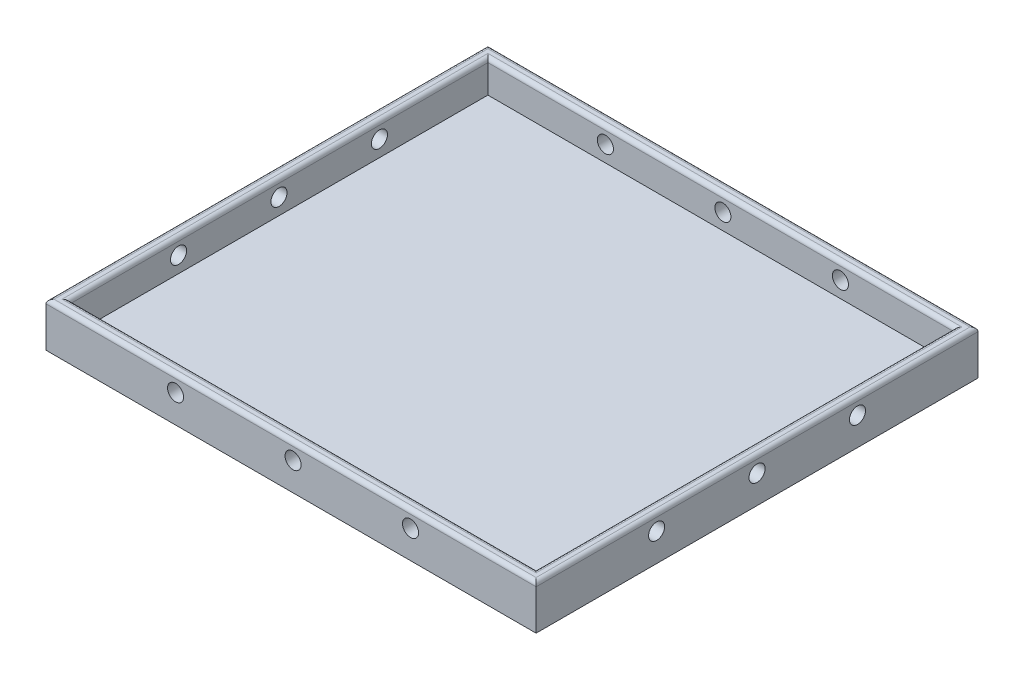
SolidWorks part; units mm, degrees
ref_plane "Front Plane" through (0, 0, 0) normal (0, 0, 1) x (1, 0, 0)
ref_plane "Top Plane" through (0, 0, 0) normal (0, 1, 0) x (1, 0, 0)
ref_plane "Right Plane" through (0, 0, 0) normal (1, 0, 0) x (0, 0, -1)
sketch "Sketch1" plane through (0, 0, 0) normal (0, 1, 0) x (1, 0, 0)
  line L1 (-201.6099, 77.8947) -> (-79.6099, 77.8947)
  line L2 (-201.6099, 77.8947) -> (-201.6099, -32.1053)
  line L3 (-201.6099, -32.1053) -> (-79.6099, -32.1053)
  line L4 (-79.6099, 77.8947) -> (-79.6099, -32.1053)
  dimension "D1" = 122
  dimension "D2" = 110
extrude "Boss-Extrude1" add sketch "Sketch1" along normal blind 11
sketch "Sketch4" plane through (0, 11, 0) normal (0, 1, 0) x (1, 0, 0)
  line L0 (-201.6099, 77.8947) -> (-201.6099, -32.1053) construction
  line L1 (-198.6099, 74.8947) -> (-82.6099, 74.8947)
  line L2 (-198.6099, 74.8947) -> (-198.6099, -29.1053)
  line L3 (-198.6099, -29.1053) -> (-82.6099, -29.1053)
  line L4 (-82.6099, 74.8947) -> (-82.6099, -29.1053)
  line L5 (-79.6099, 77.8947) -> (-201.6099, 77.8947) construction
  line L6 (-79.6099, -32.1053) -> (-79.6099, 77.8947) construction
  line L7 (-201.6099, -32.1053) -> (-79.6099, -32.1053) construction
  dimension "D1" = 3
  dimension "D2" = 3
  dimension "D3" = 3
  dimension "D4" = 3
extrude "Cut-Extrude1" cut sketch "Sketch4" against normal blind 8
sketch "Sketch5" plane through (0, 0, -74.8947) normal (0, 0, 1) x (1, 0, 0)
  line L0 (-198.6099, 3) -> (-198.6099, 11) construction
  line L1 (-82.6099, 3) -> (-198.6099, 3) construction
  circle A0 centre (-169.3599, 7) radius 2
  circle A1 centre (-140.1099, 7) radius 2
  circle A2 centre (-110.8599, 7) radius 2
  dimension "D1" = 29.25
  dimension "D2" = 29.25
  dimension "D3" = 29.25
  dimension "D4" = 4
  dimension "D5" = 4
  dimension "D6" = 4
sketch "Sketch6" plane through (-198.6099, 0, 0) normal (1, 0, 0) x (0, 0, -1)
  line L0 (-29.1053, 3) -> (-29.1053, 11) construction
  line L1 (74.8947, 3) -> (74.8947, 11) construction
  line L2 (74.8947, 3) -> (-29.1053, 3) construction
  circle A0 centre (-2.1053, 7) radius 2
  circle A1 centre (22.8947, 7) radius 2
  circle A2 centre (47.8947, 7) radius 2
  dimension "D1" = 27
  dimension "D2" = 25
  dimension "D3" = 25
  dimension "D4" = 27
  dimension "D5" = 4
extrude "Cut-Extrude6" cut sketch "Sketch6" against normal through all both and the other way through all
extrude "Cut-Extrude5" cut sketch "Sketch5" against normal through all both and the other way through all
fillet "Fillet2" radius 1 8 edges at (-140.6099, 11, 29.1053) (-140.6099, 11, 32.1053) (-79.6099, 11, -22.8947) (-82.6099, 11, -22.8947) (-198.6099, 11, -22.8947) (-140.6099, 11, -74.8947) (-201.6099, 11, -22.8947) (-140.6099, 11, -77.8947)
